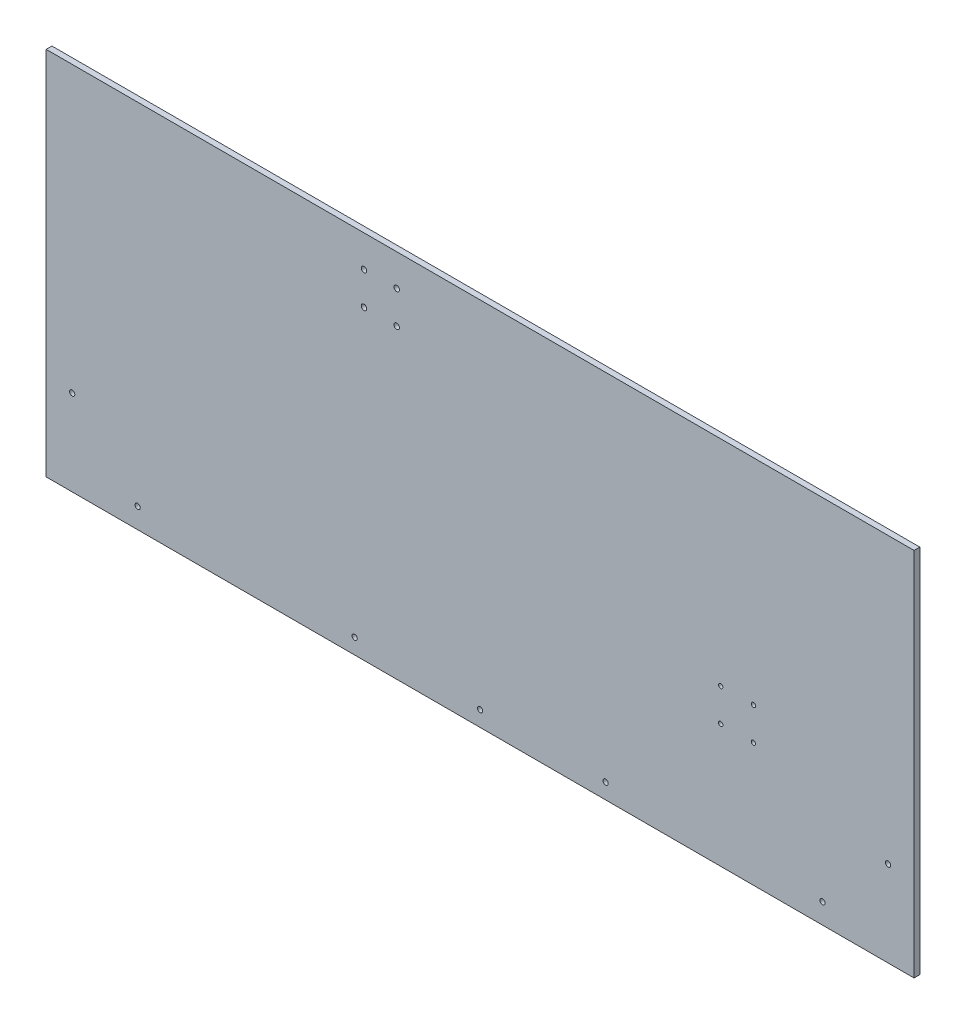
SolidWorks part; units mm, degrees
ref_plane "Front Plane" through (0, 0, 0) normal (0, 0, 1) x (1, 0, 0)
ref_plane "Top Plane" through (0, 0, 0) normal (0, 1, 0) x (1, 0, 0)
ref_plane "Right Plane" through (0, 0, 0) normal (1, 0, 0) x (0, 0, -1)
sketch "Sketch1" plane through (0, 0, 0) normal (0, 0, 1) x (1, 0, 0)
  line L1 (-357.1875, -152.4) -> (357.1875, -152.4)
  line L2 (-357.1875, -152.4) -> (-357.1875, 152.4)
  line L3 (-357.1875, 152.4) -> (357.1875, 152.4)
  line L4 (357.1875, -152.4) -> (357.1875, 152.4)
  line L5 (-357.1875, -152.4) -> (357.1875, 152.4) construction
  line L6 (-357.1875, 152.4) -> (357.1875, -152.4) construction
  point P0 (0, 0)
  dimension "D1" = 714.375
  dimension "D2" = 304.8
extrude "Boss-Extrude1" add sketch "Sketch1" along normal blind 4.7625
sketch "Sketch4" plane through (0, 0, 4.7625) normal (0, 0, 1) x (1, 0, 0)
  line L0 (0, 0) -> (0, 152.4) construction
  line L1 (357.1875, 152.4) -> (-357.1875, 152.4) construction
  line L2 (-357.1875, 146.05) -> (357.1875, 146.05) construction
  line L3 (-357.1875, 152.4) -> (-357.1875, -152.4) construction
  line L4 (357.1875, -152.4) -> (357.1875, 152.4) construction
  line L5 (-357.1875, 146.05) -> (0, 146.05) construction
  line L6 (0, 146.05) -> (357.1875, 146.05) construction
  line L7 (-357.1875, 146.05) -> (0, 146.05) construction
  line L8 (0, 146.05) -> (357.1875, 146.05) construction
  line L9 (-279.4, 103.505) -> (-279.4, 112.395) construction
  line L10 (0, 82.55) -> (357.1875, 82.55) construction
  line L11 (357.1875, 82.55) -> (-357.1875, 82.55) construction
  line L12 (279.4, 86.8616) -> (279.4, 129.0384) construction
  line L13 (279.4, 103.505) -> (279.4, 112.395) construction
  line L14 (277.1521, 103.505) -> (277.1521, 112.395)
  line L15 (281.6479, 103.505) -> (281.6479, 112.395)
  line L16 (-277.1521, 103.505) -> (-277.1521, 112.395)
  line L17 (-281.6479, 103.505) -> (-281.6479, 112.395)
  line L18 (-279.4, 107.95) -> (-279.4, 82.55) construction
  line L19 (279.4, 107.95) -> (279.4, 82.55) construction
  line L20 (-279.4, 86.8616) -> (-279.4, 129.0384) construction
  arc A0 (277.1521, 103.505) -> (281.6479, 103.505) centre (279.4, 103.505) ccw
  arc A1 (281.6479, 112.395) -> (277.1521, 112.395) centre (279.4, 112.395) ccw
  arc A2 (-277.1521, 103.505) -> (-281.6479, 103.505) centre (-279.4, 103.505) cw
  arc A3 (-281.6479, 112.395) -> (-277.1521, 112.395) centre (-279.4, 112.395) cw
  point P21 (279.4, 107.95)
  point P26 (-279.4, 107.95)
  dimension "D1" = 6.35
  dimension "D2" = 63.5
  dimension "D3" = 8.89
  dimension "D4" = 4.4958
  dimension "D6" = 279.4
  dimension "D7" = 25.4
extrude "Cut-Extrude3" cut sketch "Sketch4" against normal through all
sketch "Sketch5" plane through (0, 0, 4.7625) normal (0, 0, 1) x (1, 0, 0)
  line L0 (0, 152.4) -> (0, -152.4) construction
  line L1 (357.1875, 152.4) -> (-357.1875, 152.4) construction
  line L2 (-357.1875, -152.4) -> (357.1875, -152.4) construction
  line L3 (-357.1875, -88.9) -> (357.1875, -88.9) construction
  line L4 (-357.1875, 152.4) -> (-357.1875, -152.4) construction
  line L5 (357.1875, -152.4) -> (357.1875, 152.4) construction
  line L6 (-357.1875, -88.9) -> (-357.1875, -152.4) construction
  line L7 (-357.1875, -120.65) -> (357.1875, -120.65) construction
  line L8 (0, -152.4) -> (0, -120.65) construction
  circle A0 centre (-127, -120.65) radius 2.1527
  circle A1 centre (-215.9, -120.65) radius 2.1527
  circle A2 centre (215.9, -120.65) radius 2.1527
  circle A3 centre (127, -120.65) radius 2.1527
  dimension "D2" = 4.3053
  dimension "D1" = 63.5
  dimension "D3" = 127
  dimension "D4" = 215.9
extrude "Cut-Extrude4" cut sketch "Sketch5" against normal up to next
sketch "Sketch7" plane through (357.1875, 0, 0) normal (1, 0, 0) x (0, 0, -1)
  line L1 (-4.7625, 152.4) -> (0, 152.4)
  line L2 (-4.7625, 152.4) -> (-4.7625, -152.4)
  line L3 (-4.7625, -152.4) -> (0, -152.4)
  line L4 (0, 152.4) -> (0, -152.4)
extrude "Boss-Extrude2" add sketch "Sketch7" against normal up to next
hole_wizard "#8 Clearance Hole1" positions "Sketch9" profile "Sketch8" hole size "#8" standard "ANSI Inch"
sketch "Sketch9" plane through (0, 0, 4.7625) normal (0, 0, 1) x (1, 0, 0)
  line L3 (-281.8865, -135.743) -> (-335.768, -81.8615) construction
  line L6 (281.8865, -135.743) -> (335.768, -81.8615) construction
  point P0 (-335.768, -81.8615)
  point P2 (-281.8865, -135.743)
  point P4 (281.8865, -135.743)
  point P6 (335.768, -81.8615)
sketch "Sketch8" plane through (-335.768, -81.8615, 4.7625) normal (1, 0, 0) x (0, -1, 0)
  line L0 (0, 0) -> (0, 75.7154)
  line L1 (0, 75.7154) -> (2.1526, 74.422)
  line L2 (2.1526, 74.422) -> (2.1526, 0)
  line L5 (2.1526, 0) -> (0, 0)
  line L10 (0, 75.7154) -> (-2.1527, 74.422) construction
  line L11 (0, -6.35) -> (0, 107.95) construction
  dimension "Hole Dia." = 4.3053
  dimension "Hole Depth" = 74.422
  dimension "Drill Angle" = 118
hole_wizard "#8 Clearance Hole2" positions "Sketch12" profile "Sketch11" hole size "#8" standard "ANSI Inch"
sketch "Sketch12" plane through (0, 0, 4.7625) normal (0, 0, 1) x (1, 0, 0)
  line L0 (-357.1875, -152.4) -> (357.1875, -152.4) construction
  point P0 (-103.251, -139.7)
  point P2 (0, -139.7)
  point P4 (103.251, -139.7)
  dimension "D1" = 12.7
  dimension "D2" = 103.251
  dimension "D3" = 103.251
sketch "Sketch11" plane through (-103.251, -139.7, 4.7625) normal (1, 0, 0) x (0, -1, 0)
  line L0 (0, 0) -> (0, 75.7154)
  line L1 (0, 75.7154) -> (2.1526, 74.422)
  line L2 (2.1526, 74.422) -> (2.1526, 0)
  line L5 (2.1526, 0) -> (0, 0)
  line L10 (0, 75.7154) -> (-2.1527, 74.422) construction
  line L11 (0, -6.35) -> (0, 107.95) construction
  dimension "Hole Dia." = 4.3053
  dimension "Hole Depth" = 74.422
  dimension "Drill Angle" = 118
hole_wizard "#8 Clearance Hole3" positions "Sketch15" profile "Sketch14" hole size "#8" standard "ANSI Inch"
sketch "Sketch15" plane through (0, 0, 4.7625) normal (0, 0, 1) x (1, 0, 0)
  line L0 (357.1875, 152.4) -> (-357.1875, 152.4) construction
  line L1 (-357.1875, 152.4) -> (-357.1875, -152.4) construction
  point P0 (-95.5675, 126.238)
  point P2 (-68.6435, 126.238)
  point P4 (-95.5675, 99.314)
  point P6 (-68.6435, 99.314)
  dimension "D1" = 26.162
  dimension "D2" = 26.924
  dimension "D3" = 26.924
  dimension "D4" = 261.62
sketch "Sketch14" plane through (-95.5675, 126.238, 4.7625) normal (1, 0, 0) x (0, -1, 0)
  line L0 (0, 0) -> (0, 75.7727)
  line L1 (0, 75.7727) -> (2.2479, 74.422)
  line L2 (2.2479, 74.422) -> (2.2479, 0)
  line L5 (2.2479, 0) -> (0, 0)
  line L10 (0, 75.7727) -> (-2.2479, 74.422) construction
  line L11 (0, -6.35) -> (0, 107.95) construction
  dimension "Hole Dia." = 4.4958
  dimension "Hole Depth" = 74.422
  dimension "Drill Angle" = 118
sketch "Sketch16" plane through (0, 0, 4.7625) normal (0, 0, 1) x (1, 0, 0)
  circle A0 centre (198.0481, -23.8676) radius 1.778
  circle A1 centre (224.9889, -23.8676) radius 1.778
  circle A2 centre (224.9889, -50.8084) radius 1.778
  circle A3 centre (198.0481, -50.8084) radius 1.778
extrude "Cut-Extrude5" cut sketch "Sketch16" against normal blind 4.7625
